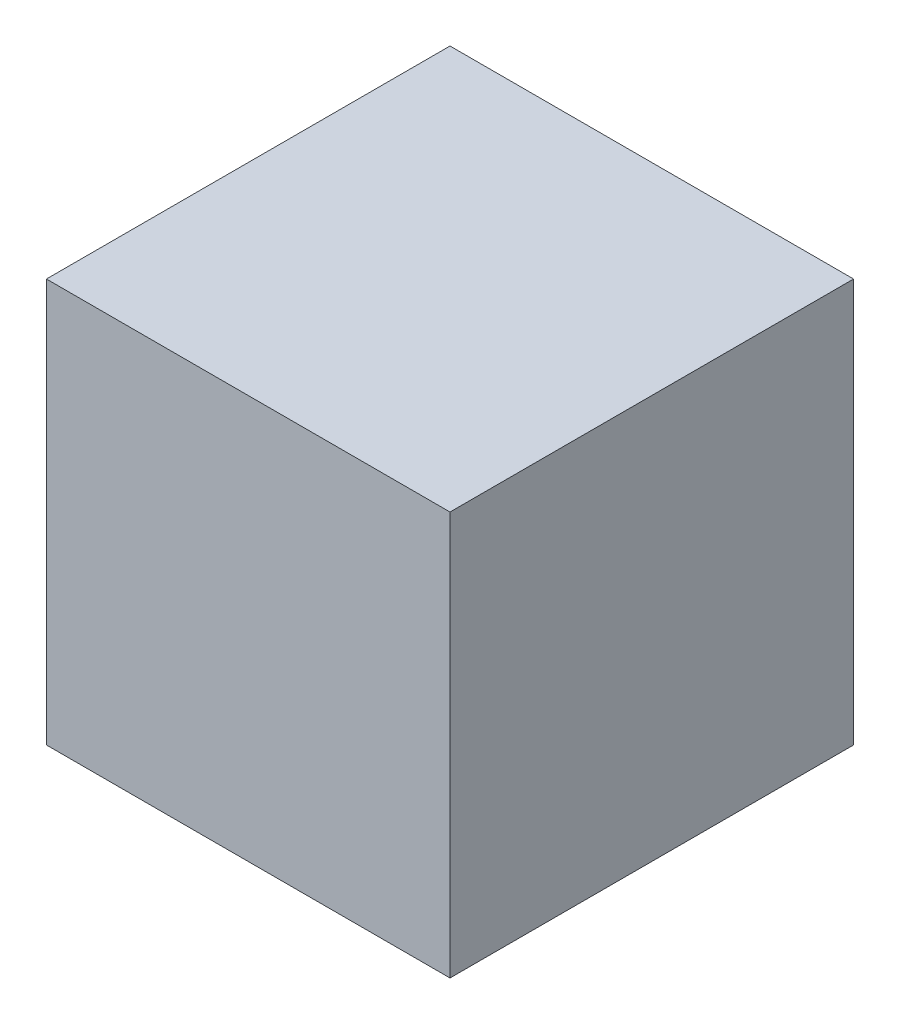
SolidWorks part; units mm, degrees
ref_plane "Front Plane" through (0, 0, 0) normal (0, 0, 1) x (1, 0, 0)
ref_plane "Top Plane" through (0, 0, 0) normal (0, 1, 0) x (1, 0, 0)
ref_plane "Right Plane" through (0, 0, 0) normal (1, 0, 0) x (0, 0, -1)
sketch "Sketch1" plane through (0, 0, 0) normal (0, 1, 0) x (1, 0, 0)
  line L1 (-12.7, -12.7) -> (12.7, -12.7)
  line L2 (-12.7, -12.7) -> (-12.7, 12.7)
  line L3 (-12.7, 12.7) -> (12.7, 12.7)
  line L4 (12.7, -12.7) -> (12.7, 12.7)
  line L5 (-12.7, -12.7) -> (12.7, 12.7) construction
  line L6 (-12.7, 12.7) -> (12.7, -12.7) construction
  point P0 (0, 0)
  dimension "D1" = 25.4
extrude "Boss-Extrude1" add sketch "Sketch1" along normal mid plane 25.4
